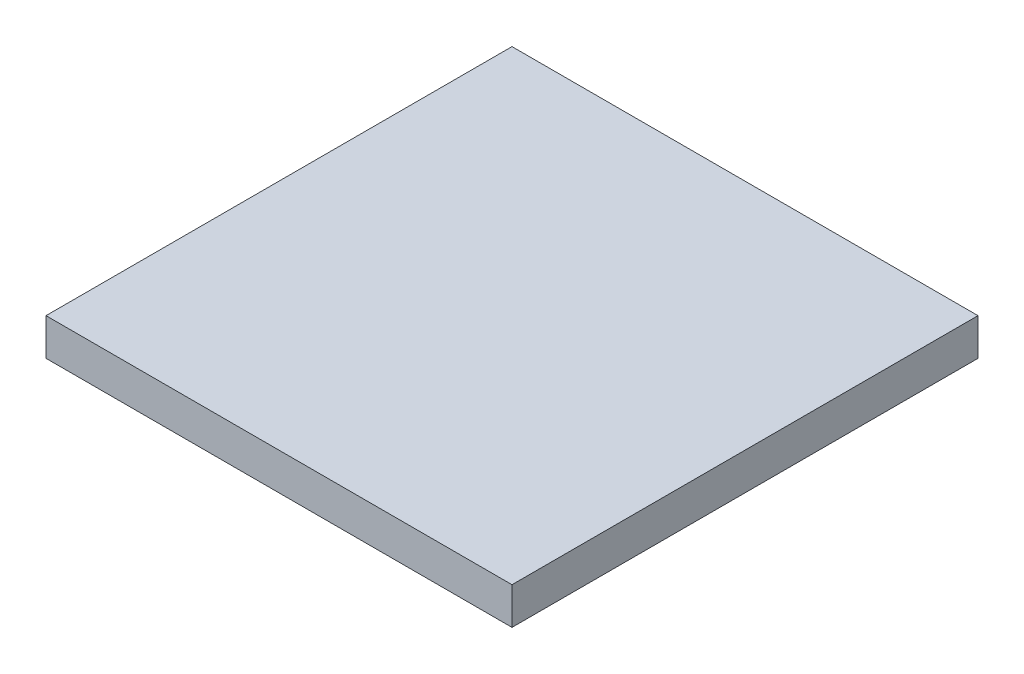
SolidWorks part; units mm, degrees
ref_plane "Front Plane" through (0, 0, 0) normal (0, 0, 1) x (1, 0, 0)
ref_plane "Top Plane" through (0, 0, 0) normal (0, 1, 0) x (1, 0, 0)
ref_plane "Right Plane" through (0, 0, 0) normal (1, 0, 0) x (0, 0, -1)
sketch "Sketch2" plane through (0, 0, 0) normal (0, 1, 0) x (1, 0, 0)
  line L1 (-50.0895, -5.1655) -> (-10.0895, -5.1655)
  line L2 (-50.0895, -5.1655) -> (-50.0895, -45.1655)
  line L3 (-50.0895, -45.1655) -> (-10.0895, -45.1655)
  line L4 (-10.0895, -5.1655) -> (-10.0895, -45.1655)
  dimension "D1" = 40
  dimension "D2" = 40
extrude "Boss-Extrude1" add sketch "Sketch2" along normal blind 3.175
